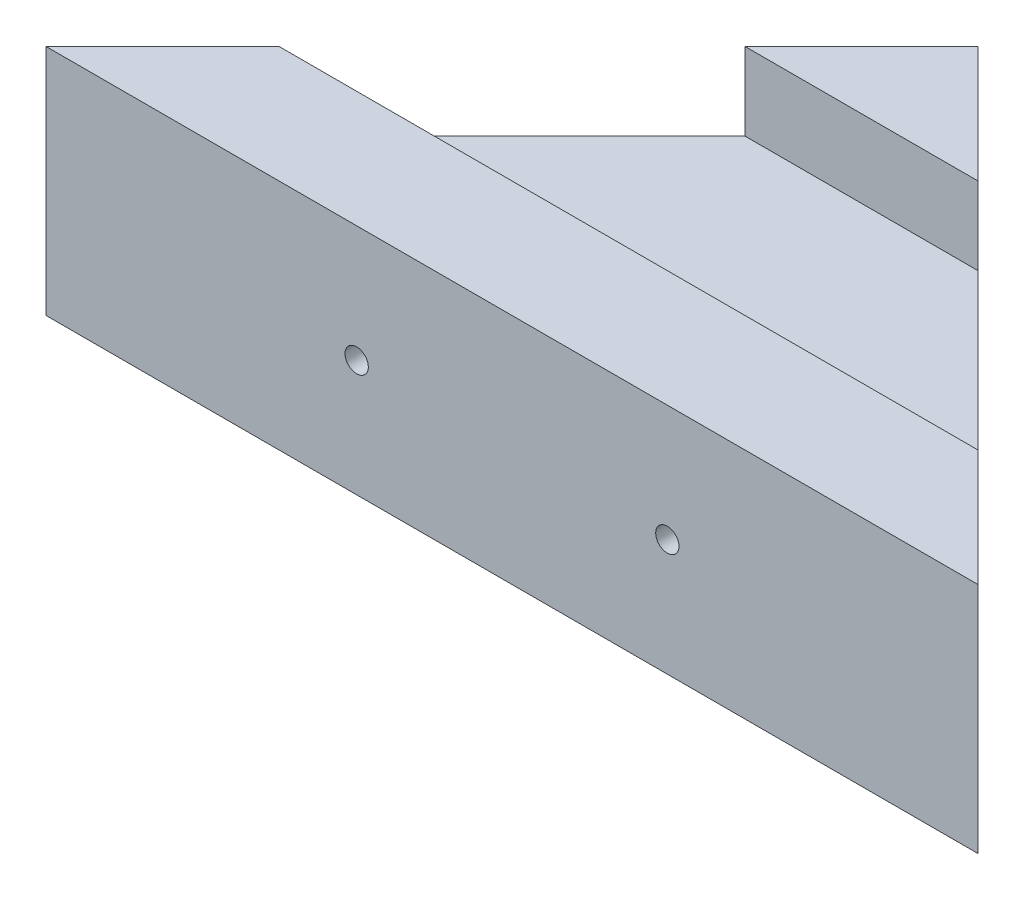
SolidWorks part; units mm, degrees
ref_plane "Front Plane" through (0, 0, 0) normal (0, 0, 1) x (1, 0, 0)
ref_plane "Top Plane" through (0, 0, 0) normal (0, 1, 0) x (1, 0, 0)
ref_plane "Right Plane" through (0, 0, 0) normal (1, 0, 0) x (0, 0, -1)
sketch "Sketch1" plane through (0, 0, 0) normal (0, 1, 0) x (1, 0, 0)
  line L0 (0, 0) -> (60, 0)
  line L1 (60, 0) -> (30, 30)
  line L2 (30, 30) -> (0, 0)
  point P5 (30, 0)
  dimension "D1" = 60
  dimension "D2" = 30
extrude "Boss-Extrude1" add sketch "Sketch1" along normal blind 15
sketch "Sketch3" plane through (0, 15, 0) normal (0, 1, 0) x (1, 0, 0)
  line L0 (7.5, 7.5) -> (52.5, 7.5)
  line L1 (30, 30) -> (0, 0) construction
  line L2 (0, 0) -> (60, 0) construction
  line L3 (60, 0) -> (30, 30) construction
  line L4 (22.5, 22.5) -> (37.5, 22.5)
  line L5 (22.5, 22.5) -> (7.5, 7.5)
  line L6 (37.5, 22.5) -> (52.5, 7.5)
  dimension "D1" = 45
  dimension "D2" = 15
extrude "Cut-Extrude1" cut sketch "Sketch3" against normal blind 5
sketch "Sketch4" plane through (0, 0, 0) normal (0, 0, 1) x (1, 0, 0)
  line L0 (0, 7.5) -> (60, 7.5) construction
  line L1 (0, 15) -> (0, 0) construction
  line L2 (60, 15) -> (60, 0) construction
  circle A0 centre (20, 7.5) radius 0.75
  circle A1 centre (40, 7.5) radius 0.75
  dimension "D1" = 1.5
  dimension "D2" = 20
  dimension "D3" = 20
extrude "Cut-Extrude2" cut sketch "Sketch4" against normal up to surface (22.5 mm away) up to face at (30, 12.5, -22.5)
